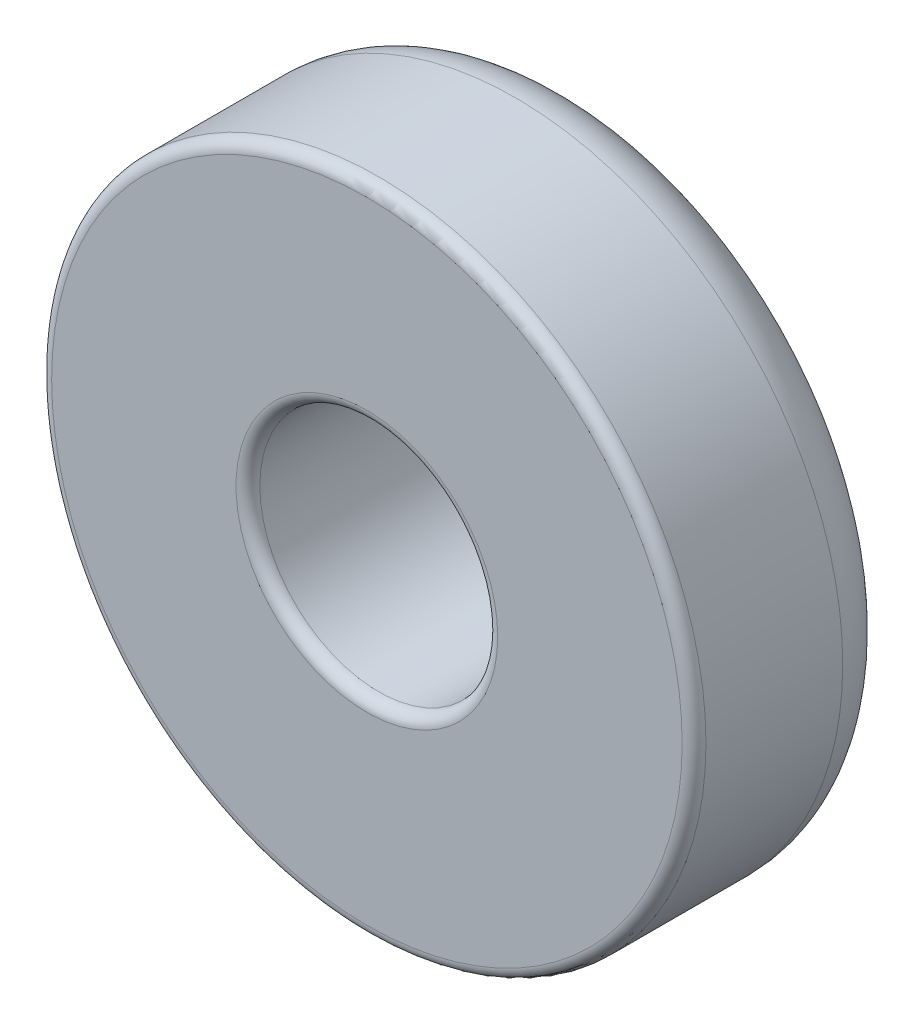
SolidWorks part; units mm, degrees
ref_plane "Front Plane" through (0, 0, 0) normal (0, 0, 1) x (1, 0, 0)
ref_plane "Top Plane" through (0, 0, 0) normal (0, 1, 0) x (1, 0, 0)
ref_plane "Right Plane" through (0, 0, 0) normal (1, 0, 0) x (0, 0, -1)
sketch "Sketch1" plane through (0, 0, 0) normal (0, 0, 1) x (1, 0, 0)
  circle A0 centre (0, 0) radius 1
  dimension "D1" = 2
extrude "Extrude-Thin1" add sketch "Sketch1" along normal blind 1.75 thin
fillet "Fillet1" radius 0.5 1 edges at (2.75, 0, 0)
fillet "Fillet2" radius 0.1 2 edges at (1, 0, 1.75) (2.75, 0, 1.75)
fillet "Fillet3" radius 0.1 1 edges at (1, 0, 0)
